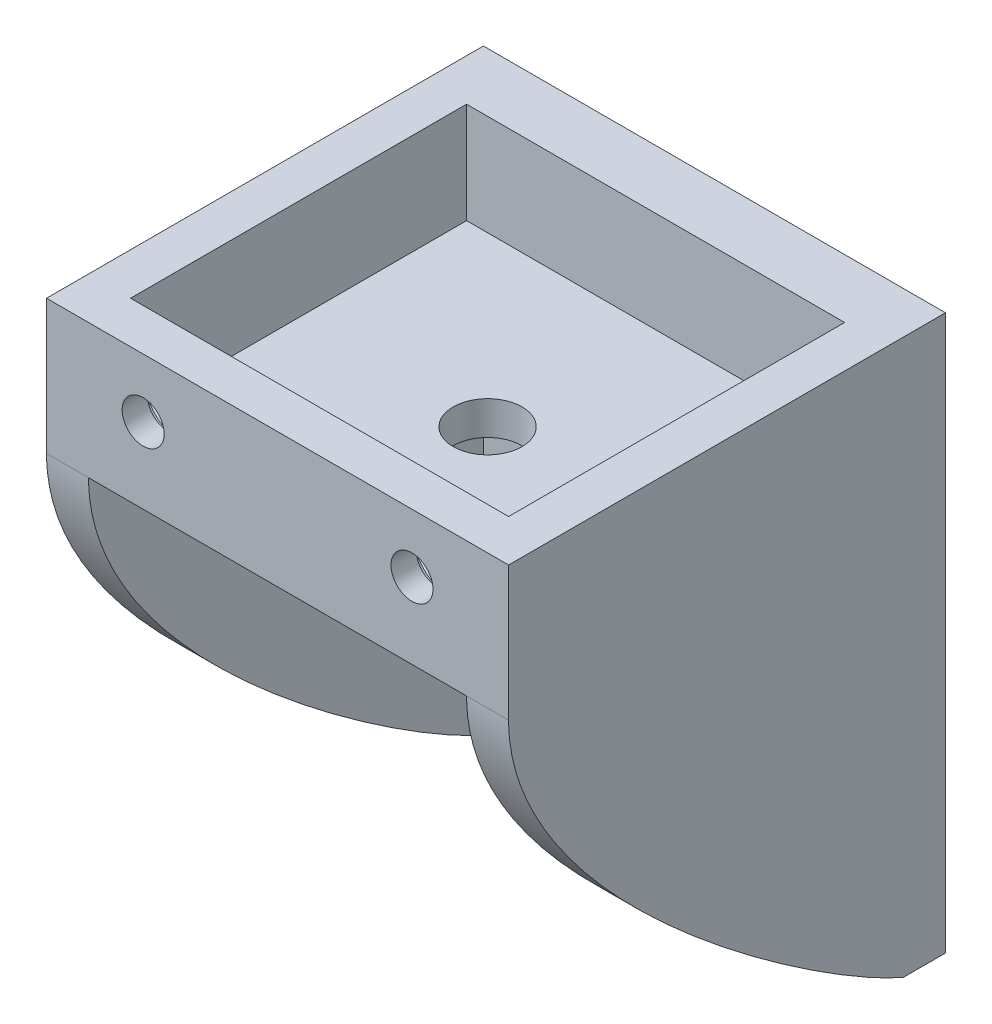
SolidWorks part; units mm, degrees
ref_plane "Front" through (0, 0, 0) normal (0, 0, 1) x (1, 0, 0)
ref_plane "Top" through (0, 0, 0) normal (0, 1, 0) x (1, 0, 0)
ref_plane "Right" through (0, 0, 0) normal (1, 0, 0) x (0, 0, -1)
sketch "Sketch1" plane through (0, 0, 0) normal (0, 0, 1) x (1, 0, 0)
  line L0 (-13.367, 0) -> (11.9353, 0) construction
  line L1 (-27.5, 25) -> (27.5, 25)
  line L2 (-27.5, 25) -> (-27.5, -25)
  line L3 (-27.5, -25) -> (27.5, -25)
  line L4 (27.5, 25) -> (27.5, -25)
  line L5 (-27.5, 25) -> (27.5, -25) construction
  line L6 (-27.5, -25) -> (27.5, 25) construction
  circle A0 centre (-17.5, -15) radius 2.5
  circle A1 centre (17.5, -15) radius 2.5
  circle A4 centre (17.5, 15) radius 2.5
  circle A5 centre (-17.5, 15) radius 2.5
  point P0 (0, 0)
  dimension "D3" = 5
  dimension "D1" = 50
  dimension "D2" = 55
  dimension "D4" = 10
  dimension "D5" = 10
extrude "Boss-Extrude1" add sketch "Sketch1" along normal blind 5
sketch "Sketch2" plane through (0, 0, 5) normal (0, 0, 1) x (1, 0, 0)
  line L0 (0, 13.5179) -> (0, -11.1851) construction
  circle A0 centre (-17.5, -15) radius 5
  circle A1 centre (17.5, -15) radius 5
  circle A3 centre (-17.5, 15) radius 5
  circle A5 centre (17.5, 15) radius 5
  circle A6 centre (-17.5, 15) radius 2.5 construction
  dimension "D1" = 10
extrude "Cut-Extrude1" cut sketch "Sketch2" against normal blind 2
sketch "Sketch3" plane through (0, 25, 0) normal (0, 1, 0) x (1, 0, 0)
  line L1 (-27.5, 0) -> (27.5, 0)
  line L2 (-27.5, 0) -> (-27.5, -52)
  line L3 (-27.5, -52) -> (27.5, -52)
  line L4 (27.5, 0) -> (27.5, -52)
  dimension "D1" = 52
extrude "Boss-Extrude2" add sketch "Sketch3" along normal blind 16
sketch "Sketch4" plane through (0, 25, 0) normal (0, -1, 0) x (-1, 0, 0)
  line L0 (27.5, -5) -> (-27.5, -5) construction
  circle A0 centre (0, -27) radius 4.1
  dimension "D1" = 22
  dimension "D2" = 8.2
extrude "Cut-Extrude2" cut sketch "Sketch4" against normal through all
sketch "Sketch5" plane through (-27.5, 0, 0) normal (-1, 0, 0) x (0, 0, 1)
  line L0 (5, -25) -> (5, 25)
  line L1 (5, 25) -> (52, 25)
  spline S0 degree 3 poles (52, 25) (52, 4.233) (15.2666, -20.7199) (5, -25) knots 0 0 0 0 0.911488 0.911488 0.911488 0.911488
extrude "Boss-Extrude3" add sketch "Sketch5" against normal blind 5
mirror "Mirror1" about plane through (0, 0, 0) normal (1, 0, 0) of "Boss-Extrude3"
sketch "Sketch6" plane through (0, 41, 0) normal (0, 1, 0) x (1, 0, 0)
  line L1 (-22.5, -7) -> (22.5, -7)
  line L2 (-22.5, -7) -> (-22.5, -47)
  line L3 (-22.5, -47) -> (22.5, -47)
  line L4 (22.5, -7) -> (22.5, -47)
  line L5 (-22.5, -7) -> (22.5, -47) construction
  line L6 (-22.5, -47) -> (22.5, -7) construction
  point P0 (0, -27)
  dimension "D1" = 40
  dimension "D2" = 45
extrude "Cut-Extrude3" cut sketch "Sketch6" against normal blind 12
sketch "Sketch8" plane through (0, 0, 52) normal (0, 0, 1) x (1, 0, 0)
  line L0 (-27.5, 41) -> (27.5, 41) construction
  line L1 (27.5, 41) -> (27.5, 25) construction
  line L2 (0, 40.3655) -> (0, 13.7518) construction
  circle A0 centre (16, 34) radius 2.5
  circle A1 centre (-16, 34) radius 2.5
  dimension "D1" = 5
  dimension "D2" = 7
  dimension "D3" = 11.5
extrude "Cut-Extrude5" cut sketch "Sketch8" against normal blind 5
sketch "Sketch10" plane through (0, 0, 47) normal (0, 0, -1) x (-1, 0, 0)
  line L0 (-27.5, 41) -> (27.5, 41) construction
  line L1 (-27.5, -25) -> (-27.5, 41) construction
  line L2 (0, 40.623) -> (0, 10.3177) construction
  circle A0 centre (-16, 34) radius 5
  circle A1 centre (16, 34) radius 5
  dimension "D1" = 7
  dimension "D3" = 10
  dimension "D2" = 11.5
extrude "Cut-Extrude6" cut sketch "Sketch10" against normal blind 2
